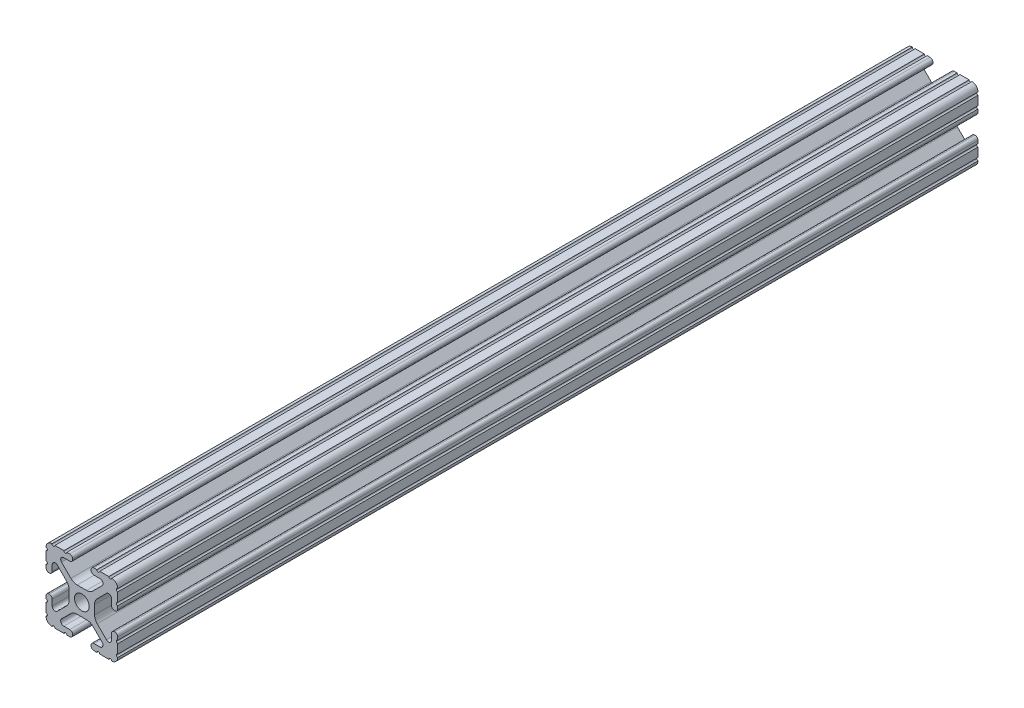
SolidWorks part; units mm, degrees
material "McMaster 6105-T5"
ref_plane "Front Plane" through (0, 0, 0) normal (0, 0, 1) x (1, 0, 0)
ref_plane "Top Plane" through (0, 0, 0) normal (0, 1, 0) x (1, 0, 0)
ref_plane "Right Plane" through (0, 0, 0) normal (1, 0, 0) x (0, 0, -1)
sketch "Sketch1" plane through (0, 0, 0) normal (0, 0, 1) x (1, 0, 0)
  line L88 (-7.1797, -8.6452) -> (-3.9523, -5.4237)
  line L89 (-1.7093, -4.4958) -> (1.7093, -4.4958)
  line L90 (3.9523, -5.4237) -> (7.1797, -8.6452)
  line L91 (6.4164, -10.4902) -> (4.2875, -10.4902)
  line L92 (3.2385, -11.5392) -> (3.2385, -11.651)
  line L93 (4.2875, -12.7) -> (5.3171, -12.7)
  line L94 (6.3331, -12.7) -> (9.5504, -12.7)
  line L95 (12.7, -9.5504) -> (12.7, -6.3331)
  line L96 (12.7, -5.3171) -> (12.7, -4.2875)
  line L97 (11.651, -3.2385) -> (11.5392, -3.2385)
  line L98 (10.4902, -4.2875) -> (10.4902, -6.4021)
  line L99 (8.7371, -7.1294) -> (5.441, -3.8408)
  line L100 (4.5085, -1.5932) -> (4.5085, 1.5932)
  line L101 (5.441, 3.8408) -> (8.7371, 7.1294)
  line L102 (10.4902, 6.4021) -> (10.4902, 4.2875)
  line L103 (11.5392, 3.2385) -> (11.651, 3.2385)
  line L104 (12.7, 4.2875) -> (12.7, 5.3171)
  line L105 (12.7, 6.3331) -> (12.7, 9.5504)
  line L106 (9.5504, 12.7) -> (6.3331, 12.7)
  line L107 (5.3171, 12.7) -> (4.2875, 12.7)
  line L108 (3.2385, 11.651) -> (3.2385, 11.5392)
  line L109 (4.2875, 10.4902) -> (6.4768, 10.4902)
  line L110 (7.207, 8.7244) -> (3.8983, 5.4232)
  line L111 (1.6558, 4.4958) -> (-1.6558, 4.4958)
  line L112 (-3.8983, 5.4232) -> (-7.207, 8.7244)
  line L113 (-6.4768, 10.4902) -> (-4.2875, 10.4902)
  line L114 (-3.2385, 11.5392) -> (-3.2385, 11.651)
  line L115 (-4.2875, 12.7) -> (-5.3171, 12.7)
  line L116 (-6.3331, 12.7) -> (-9.5504, 12.7)
  line L117 (-12.7, 9.5504) -> (-12.7, 6.3331)
  line L118 (-12.7, 5.3171) -> (-12.7, 4.2875)
  line L119 (-11.651, 3.2385) -> (-11.5392, 3.2385)
  line L120 (-10.4902, 4.2875) -> (-10.4902, 6.4021)
  line L121 (-8.7371, 7.1294) -> (-5.441, 3.8408)
  line L122 (-4.5085, 1.5932) -> (-4.5085, -1.5932)
  line L123 (-5.441, -3.8408) -> (-8.7371, -7.1294)
  line L124 (-10.4902, -6.4021) -> (-10.4902, -4.2875)
  line L125 (-11.5392, -3.2385) -> (-11.651, -3.2385)
  line L126 (-12.7, -4.2875) -> (-12.7, -5.3171)
  line L127 (-12.7, -6.3331) -> (-12.7, -9.5504)
  line L128 (-9.5504, -12.7) -> (-6.3331, -12.7)
  line L129 (-5.3171, -12.7) -> (-4.2875, -12.7)
  line L130 (-3.2385, -11.651) -> (-3.2385, -11.5392)
  line L131 (-4.2875, -10.4902) -> (-6.4164, -10.4902)
  circle A1 centre (0, 0) radius 2.6035
  arc A104 (-7.1797, -8.6452) -> (-6.4164, -10.4902) centre (-6.4164, -9.4098) ccw
  arc A105 (-1.7093, -4.4958) -> (-3.9523, -5.4237) centre (-1.7093, -7.6708) ccw
  arc A106 (3.9523, -5.4237) -> (1.7093, -4.4958) centre (1.7093, -7.6708) ccw
  arc A107 (6.4164, -10.4902) -> (7.1797, -8.6452) centre (6.4164, -9.4098) ccw
  arc A108 (4.2875, -10.4902) -> (3.2385, -11.5392) centre (4.2875, -11.5392) ccw
  arc A109 (3.2385, -11.651) -> (4.2875, -12.7) centre (4.2875, -11.651) ccw
  arc A110 (6.3331, -12.7) -> (5.3171, -12.7) centre (5.8251, -12.7) ccw
  arc A111 (10.5664, -12.6998) -> (9.5504, -12.7) centre (10.0584, -12.7) ccw
  arc A112 (10.5664, -12.6998) -> (12.6998, -10.5664) centre (10.5918, -10.5918) ccw
  arc A113 (12.7, -9.5504) -> (12.6998, -10.5664) centre (12.7, -10.0584) ccw
  arc A114 (12.7, -5.3171) -> (12.7, -6.3331) centre (12.7, -5.8251) ccw
  arc A115 (12.7, -4.2875) -> (11.651, -3.2385) centre (11.651, -4.2875) ccw
  arc A116 (11.5392, -3.2385) -> (10.4902, -4.2875) centre (11.5392, -4.2875) ccw
  arc A117 (8.7371, -7.1294) -> (10.4902, -6.4021) centre (9.4628, -6.4021) ccw
  arc A118 (4.5085, -1.5932) -> (5.441, -3.8408) centre (7.6835, -1.5932) ccw
  arc A119 (5.441, 3.8408) -> (4.5085, 1.5932) centre (7.6835, 1.5932) ccw
  arc A120 (10.4902, 6.4021) -> (8.7371, 7.1294) centre (9.4628, 6.4021) ccw
  arc A121 (10.4902, 4.2875) -> (11.5392, 3.2385) centre (11.5392, 4.2875) ccw
  arc A122 (11.651, 3.2385) -> (12.7, 4.2875) centre (11.651, 4.2875) ccw
  arc A123 (12.7, 6.3331) -> (12.7, 5.3171) centre (12.7, 5.8251) ccw
  arc A124 (12.6998, 10.5664) -> (12.7, 9.5504) centre (12.7, 10.0584) ccw
  arc A125 (12.6998, 10.5664) -> (10.5664, 12.6998) centre (10.5918, 10.5918) ccw
  arc A126 (9.5504, 12.7) -> (10.5664, 12.6998) centre (10.0584, 12.7) ccw
  arc A127 (5.3171, 12.7) -> (6.3331, 12.7) centre (5.8251, 12.7) ccw
  arc A128 (4.2875, 12.7) -> (3.2385, 11.651) centre (4.2875, 11.651) ccw
  arc A129 (3.2385, 11.5392) -> (4.2875, 10.4902) centre (4.2875, 11.5392) ccw
  arc A130 (7.207, 8.7244) -> (6.4768, 10.4902) centre (6.4768, 9.4563) ccw
  arc A131 (1.6558, 4.4958) -> (3.8983, 5.4232) centre (1.6558, 7.6708) ccw
  arc A132 (-3.8983, 5.4232) -> (-1.6558, 4.4958) centre (-1.6558, 7.6708) ccw
  arc A133 (-6.4768, 10.4902) -> (-7.207, 8.7244) centre (-6.4768, 9.4563) ccw
  arc A134 (-4.2875, 10.4902) -> (-3.2385, 11.5392) centre (-4.2875, 11.5392) ccw
  arc A135 (-3.2385, 11.651) -> (-4.2875, 12.7) centre (-4.2875, 11.651) ccw
  arc A136 (-6.3331, 12.7) -> (-5.3171, 12.7) centre (-5.8251, 12.7) ccw
  arc A137 (-10.5664, 12.6998) -> (-9.5504, 12.7) centre (-10.0584, 12.7) ccw
  arc A138 (-10.5664, 12.6998) -> (-12.6998, 10.5664) centre (-10.5918, 10.5918) ccw
  arc A139 (-12.7, 9.5504) -> (-12.6998, 10.5664) centre (-12.7, 10.0584) ccw
  arc A140 (-12.7, 5.3171) -> (-12.7, 6.3331) centre (-12.7, 5.8251) ccw
  arc A141 (-12.7, 4.2875) -> (-11.651, 3.2385) centre (-11.651, 4.2875) ccw
  arc A142 (-11.5392, 3.2385) -> (-10.4902, 4.2875) centre (-11.5392, 4.2875) ccw
  arc A143 (-8.7371, 7.1294) -> (-10.4902, 6.4021) centre (-9.4628, 6.4021) ccw
  arc A144 (-4.5085, 1.5932) -> (-5.441, 3.8408) centre (-7.6835, 1.5932) ccw
  arc A145 (-5.441, -3.8408) -> (-4.5085, -1.5932) centre (-7.6835, -1.5932) ccw
  arc A146 (-10.4902, -6.4021) -> (-8.7371, -7.1294) centre (-9.4628, -6.4021) ccw
  arc A147 (-10.4902, -4.2875) -> (-11.5392, -3.2385) centre (-11.5392, -4.2875) ccw
  arc A148 (-11.651, -3.2385) -> (-12.7, -4.2875) centre (-11.651, -4.2875) ccw
  arc A149 (-12.7, -6.3331) -> (-12.7, -5.3171) centre (-12.7, -5.8251) ccw
  arc A150 (-12.6998, -10.5664) -> (-12.7, -9.5504) centre (-12.7, -10.0584) ccw
  arc A151 (-12.6998, -10.5664) -> (-10.5664, -12.6998) centre (-10.5918, -10.5918) ccw
  arc A152 (-9.5504, -12.7) -> (-10.5664, -12.6998) centre (-10.0584, -12.7) ccw
  arc A153 (-5.3171, -12.7) -> (-6.3331, -12.7) centre (-5.8251, -12.7) ccw
  arc A154 (-4.2875, -12.7) -> (-3.2385, -11.651) centre (-4.2875, -11.651) ccw
  arc A155 (-3.2385, -11.5392) -> (-4.2875, -10.4902) centre (-4.2875, -11.5392) ccw
extrude "Boss-Extrude1" add sketch "Sketch1" along normal mid plane 304.8
sketch "Sketch2" plane through (0, 12.7, 0) normal (0, 1, 0) x (1, 0, 0)
  line L0 (0, -155.4789) -> (0, 151.1822) construction
  line L1 (1.6558, -152.4) -> (-1.6558, -152.4) construction
  line L2 (1.6558, 152.4) -> (-1.6558, 152.4) construction
  circle A0 centre (0, -88.9) radius 3.175
  circle A1 centre (0, 127) radius 3.175
  point P4 (0, -152.4)
  point P12 (0, 152.4)
  dimension "D3" = 6.35
  dimension "D1" = 63.5
  dimension "D2" = 25.4
extrude "Cut-Extrude1" cut sketch "Sketch2" against normal through all both and the other way through all
sketch "Sketch3" plane through (-12.7, 0, 0) normal (-1, 0, 0) x (0, 0, 1)
  line L0 (-144.1574, 0) -> (-126.6701, 0) construction
  line L2 (152.4, 1.5932) -> (152.4, -1.5932) construction
  line L3 (-152.4, 1.5932) -> (-152.4, -1.5932) construction
  circle A0 centre (-101.6, 0) radius 3.175
  circle A1 centre (63.5, 0) radius 3.175
  dimension "D1" = 6.35
  dimension "D2" = 88.9
  dimension "D3" = 50.8
extrude "Cut-Extrude2" cut sketch "Sketch3" against normal through all both and the other way through all
